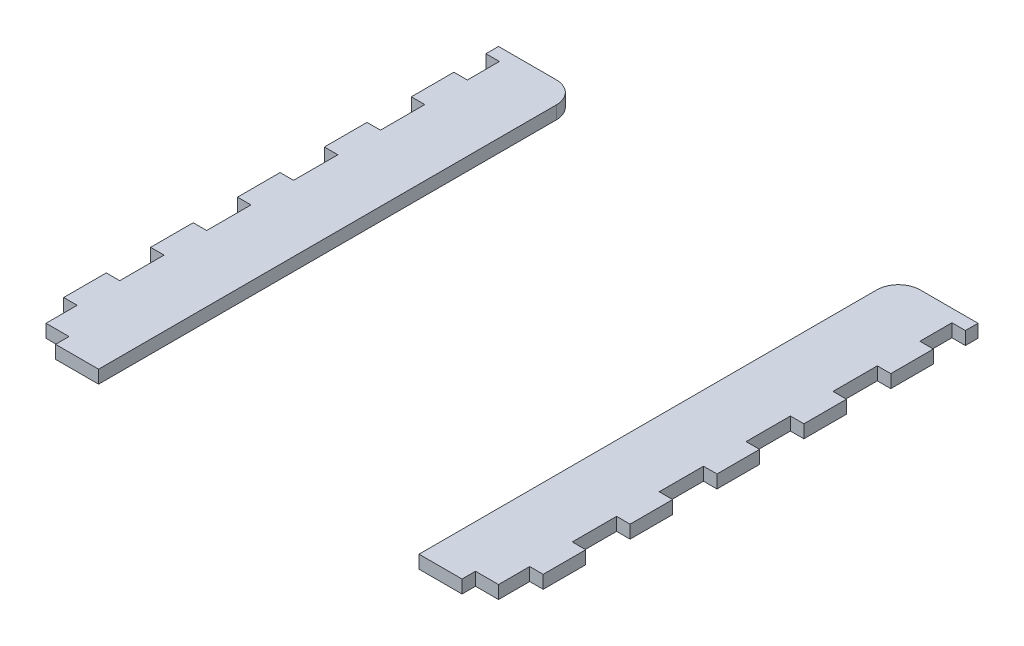
SolidWorks part; units mm, degrees
ref_plane "Front Plane" through (0, 0, 0) normal (0, 0, 1) x (1, 0, 0)
ref_plane "Top Plane" through (0, 0, 0) normal (0, 1, 0) x (1, 0, 0)
ref_plane "Right Plane" through (0, 0, 0) normal (1, 0, 0) x (0, 0, -1)
sketch "Sketch1" plane through (0, 0, 0) normal (0, 1, 0) x (1, 0, 0)
  line L0 (0, 0) -> (0, 21) construction
  line L1 (-36.8722, 43.5014) -> (-36.8722, -66.843) construction
  line L2 (36.8722, 43.5014) -> (36.8722, -66.843) construction
  line L3 (55.1722, 43.5014) -> (55.1722, -66.843) construction
  line L4 (-55.1722, -66.843) -> (55.1722, -66.843) construction
  line L5 (-55.1722, 43.5014) -> (-55.1722, -66.843) construction
  line L6 (-55.1722, 43.5014) -> (55.1722, 43.5014) construction
  line L7 (-36.8722, 38.5014) -> (-36.8722, -66.843)
  line L8 (36.8722, 38.5014) -> (36.8722, -66.843)
  line L9 (55.1722, 43.5014) -> (55.1722, -66.843)
  line L10 (-55.1722, -66.843) -> (-36.8722, -66.843)
  line L11 (-55.1722, 43.5014) -> (-55.1722, -66.843)
  line L12 (-55.1722, 43.5014) -> (-41.8722, 43.5014)
  line L13 (41.8722, 43.5014) -> (55.1722, 43.5014)
  line L14 (36.8722, -66.843) -> (55.1722, -66.843)
  circle A0 centre (0, 0) radius 21 construction
  circle A1 centre (0, 0) radius 21 construction
  arc A2 (-36.8722, 38.5014) -> (-41.8722, 43.5014) centre (-41.8722, 38.5014) ccw
  arc A3 (36.8722, 38.5014) -> (41.8722, 43.5014) centre (41.8722, 38.5014) cw
  dimension "D1" = 5
extrude "Boss-Extrude1" add sketch "Sketch1" against normal up to vertex (3 mm away)
sketch "Sketch2" plane through (0, 0, 0) normal (0, 1, 0) x (1, 0, 0)
  line L0 (15, -58.743) -> (15, -55.743) construction
  line L1 (25, -58.743) -> (25, -55.743) construction
  line L2 (15, -58.743) -> (15, -55.743) construction
  line L3 (25, -58.743) -> (25, -55.743) construction
  line L4 (55.2722, 3.4292) -> (52.0722, 3.4292)
  line L5 (52.0722, 3.4292) -> (52.0722, -6.7708)
  line L6 (52.0722, -6.7708) -> (55.2722, -6.7708)
  line L7 (55.2722, -6.7708) -> (55.2722, 3.4292)
  line L8 (55.2722, 3.4292) -> (52.0722, 3.4292)
  line L9 (52.0722, 3.4292) -> (52.0722, -6.7708)
  line L10 (52.0722, -6.7708) -> (55.2722, -6.7708)
  line L11 (55.2722, -6.7708) -> (55.2722, 3.4292)
  line L12 (52.0722, 13.2292) -> (55.2722, 13.2292)
  line L13 (55.2722, 13.2292) -> (55.2722, 23.4292)
  line L14 (55.2722, 23.4292) -> (52.0722, 23.4292)
  line L15 (52.0722, 23.4292) -> (52.0722, 13.2292)
  line L16 (52.0722, 13.2292) -> (55.2722, 13.2292)
  line L17 (55.2722, 13.2292) -> (55.2722, 23.4292)
  line L18 (55.2722, 23.4292) -> (52.0722, 23.4292)
  line L19 (52.0722, 23.4292) -> (52.0722, 13.2292)
  line L20 (55.2722, -26.7708) -> (55.2722, -16.5708)
  line L21 (55.2722, -16.5708) -> (52.0722, -16.5708)
  line L22 (52.0722, -16.5708) -> (52.0722, -26.7708)
  line L23 (52.0722, -26.7708) -> (55.2722, -26.7708)
  line L24 (55.2722, -26.7708) -> (55.2722, -16.5708)
  line L25 (55.2722, -16.5708) -> (52.0722, -16.5708)
  line L26 (52.0722, -16.5708) -> (52.0722, -26.7708)
  line L27 (52.0722, -26.7708) -> (55.2722, -26.7708)
  line L44 (-55.2722, 13.2292) -> (-52.0722, 13.2292)
  line L45 (-52.0722, 13.2292) -> (-52.0722, 23.4292)
  line L46 (-52.0722, 23.4292) -> (-55.2722, 23.4292)
  line L47 (-55.2722, 23.4292) -> (-55.2722, 13.2292)
  line L48 (-55.2722, 13.2292) -> (-52.0722, 13.2292)
  line L49 (-52.0722, 13.2292) -> (-52.0722, 23.4292)
  line L50 (-52.0722, 23.4292) -> (-55.2722, 23.4292)
  line L51 (-55.2722, 23.4292) -> (-55.2722, 13.2292)
  line L52 (-52.0722, 3.4292) -> (-55.2722, 3.4292)
  line L53 (-55.2722, 3.4292) -> (-55.2722, -6.7708)
  line L54 (-55.2722, -6.7708) -> (-52.0722, -6.7708)
  line L55 (-52.0722, -6.7708) -> (-52.0722, 3.4292)
  line L56 (-52.0722, 3.4292) -> (-55.2722, 3.4292)
  line L57 (-55.2722, 3.4292) -> (-55.2722, -6.7708)
  line L58 (-55.2722, -6.7708) -> (-52.0722, -6.7708)
  line L59 (-52.0722, -6.7708) -> (-52.0722, 3.4292)
  line L60 (55.2722, 40.6014) -> (52.0722, 40.6014)
  line L61 (55.2722, 33.2292) -> (55.2722, 40.6014)
  line L62 (52.0722, 33.2292) -> (55.2722, 33.2292)
  line L63 (52.0722, 40.6014) -> (52.0722, 33.2292)
  line L64 (55.2722, 40.6014) -> (52.0722, 40.6014)
  line L65 (55.2722, 33.2292) -> (55.2722, 40.6014)
  line L66 (52.0722, 33.2292) -> (55.2722, 33.2292)
  line L67 (52.0722, 40.6014) -> (52.0722, 33.2292)
  line L68 (-55.2722, -26.7708) -> (-52.0722, -26.7708)
  line L69 (-52.0722, -26.7708) -> (-52.0722, -16.5708)
  line L70 (-52.0722, -16.5708) -> (-55.2722, -16.5708)
  line L71 (-55.2722, -16.5708) -> (-55.2722, -26.7708)
  line L72 (-55.2722, -26.7708) -> (-52.0722, -26.7708)
  line L73 (-52.0722, -26.7708) -> (-52.0722, -16.5708)
  line L74 (-52.0722, -16.5708) -> (-55.2722, -16.5708)
  line L75 (-55.2722, -16.5708) -> (-55.2722, -26.7708)
  line L76 (55.2722, -36.5708) -> (52.0722, -36.5708)
  line L77 (52.0722, -36.5708) -> (52.0722, -46.7708)
  line L78 (52.0722, -46.7708) -> (55.2722, -46.7708)
  line L79 (55.2722, -46.7708) -> (55.2722, -36.5708)
  line L80 (55.2722, -36.5708) -> (52.0722, -36.5708)
  line L81 (52.0722, -36.5708) -> (52.0722, -46.7708)
  line L82 (52.0722, -46.7708) -> (55.2722, -46.7708)
  line L83 (55.2722, -46.7708) -> (55.2722, -36.5708)
  line L86 (44.9, -66.943) -> (55.2722, -66.943)
  line L87 (55.2722, -66.943) -> (55.2722, -56.5708)
  line L88 (55.2722, -56.5708) -> (52.0722, -56.5708)
  line L89 (52.0722, -56.5708) -> (52.0722, -63.743)
  line L90 (52.0722, -63.743) -> (44.9, -63.743)
  line L91 (44.9, -63.743) -> (44.9, -66.943)
  line L92 (46.7722, -66.943) -> (55.2722, -66.943)
  line L93 (55.2722, -66.943) -> (55.2722, -56.5708)
  line L94 (55.2722, -56.5708) -> (52.0722, -56.5708)
  line L95 (52.0722, -56.5708) -> (52.0722, -63.743)
  line L96 (52.0722, -63.743) -> (46.7722, -63.743)
  line L97 (46.7722, -63.743) -> (46.7722, -66.943)
  line L104 (-52.0722, 40.6014) -> (-55.2722, 40.6014)
  line L105 (-55.2722, 40.6014) -> (-55.2722, 33.2292)
  line L106 (-55.2722, 33.2292) -> (-52.0722, 33.2292)
  line L107 (-52.0722, 33.2292) -> (-52.0722, 40.6014)
  line L108 (-52.0722, 40.6014) -> (-55.2722, 40.6014)
  line L109 (-55.2722, 40.6014) -> (-55.2722, 33.2292)
  line L110 (-55.2722, 33.2292) -> (-52.0722, 33.2292)
  line L111 (-52.0722, 33.2292) -> (-52.0722, 40.6014)
  line L112 (-55.2722, -46.7708) -> (-52.0722, -46.7708)
  line L113 (-55.2722, -36.5708) -> (-55.2722, -46.7708)
  line L114 (-52.0722, -36.5708) -> (-55.2722, -36.5708)
  line L115 (-52.0722, -46.7708) -> (-52.0722, -36.5708)
  line L116 (-55.2722, -46.7708) -> (-52.0722, -46.7708)
  line L117 (-55.2722, -36.5708) -> (-55.2722, -46.7708)
  line L118 (-52.0722, -36.5708) -> (-55.2722, -36.5708)
  line L119 (-52.0722, -46.7708) -> (-52.0722, -36.5708)
  line L122 (0, -11.6708) -> (0, 43.5014) construction
  line L123 (0, -11.6708) -> (0, 43.5014) construction
  line L124 (-46.7722, -66.943) -> (-55.2722, -66.943)
  line L125 (-46.7722, -63.743) -> (-46.7722, -66.943)
  line L126 (-52.0722, -63.743) -> (-46.7722, -63.743)
  line L127 (-52.0722, -56.5708) -> (-52.0722, -63.743)
  line L128 (-55.2722, -56.5708) -> (-52.0722, -56.5708)
  line L129 (-55.2722, -66.943) -> (-55.2722, -56.5708)
  line L140 (15, -58.743) -> (25, -58.743) construction
  line L141 (25, -55.743) -> (15, -55.743) construction
  line L142 (36.8722, 38.5014) -> (36.8722, -66.843) construction
  line L143 (36.8722, 38.5014) -> (36.8722, -66.843) construction
  line L144 (36.8722, -66.843) -> (46.8722, -66.843) construction
  line L145 (46.8722, -66.843) -> (46.8722, -63.843) construction
  line L146 (46.8722, -63.843) -> (36.8722, -63.843) construction
  line L147 (46.7722, -65.343) -> (46.8722, -65.343) construction
  line L148 (46.8722, -66.843) -> (46.8722, -66.943) construction
  dimension "D1" = 0
  dimension "D2" = 0
  dimension "D3" = 0
  dimension "D6" = 0
  dimension "D7" = 0
  dimension "D8" = 0
  dimension "D9" = 0
  dimension "D10" = 0
  dimension "D11" = 0
  dimension "D13" = 0
  dimension "D14" = 0
extrude "Cut-Extrude1" cut sketch "Sketch2" against normal through all
